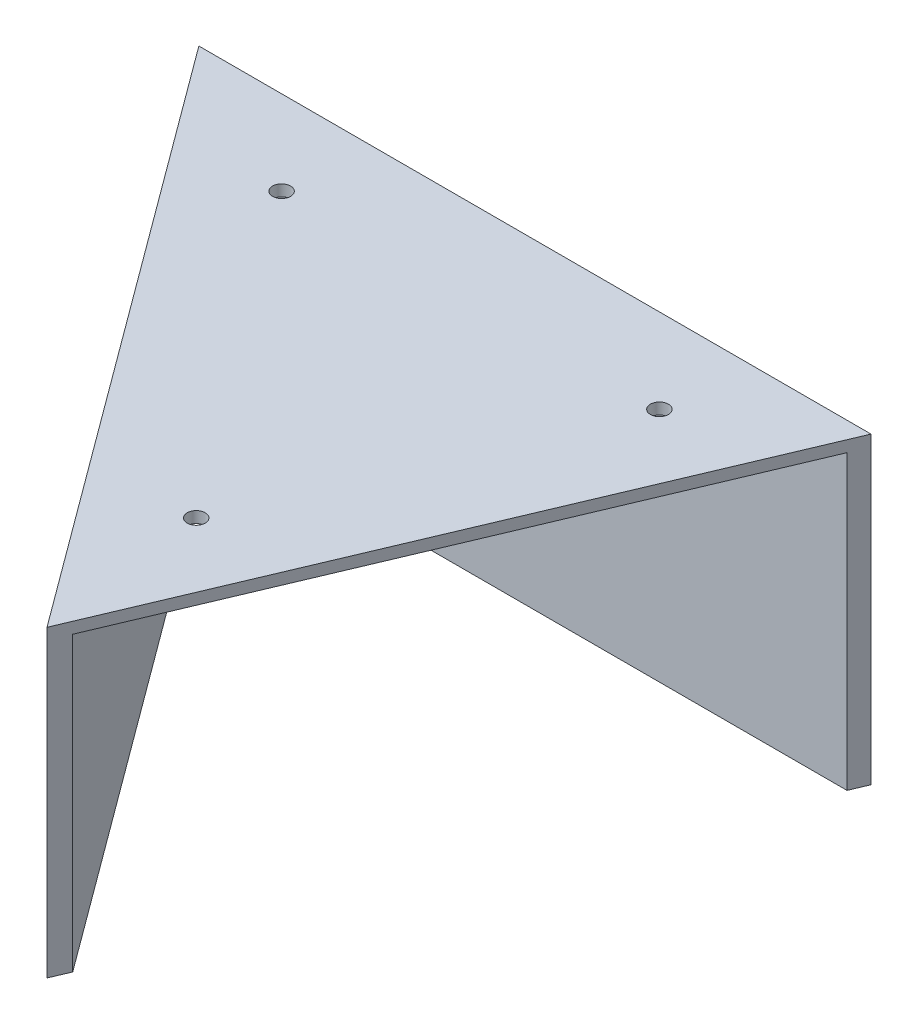
SolidWorks part; units mm, degrees
ref_plane "Front Plane" through (0, 0, 0) normal (0, 0, 1) x (1, 0, 0)
ref_plane "Top Plane" through (0, 0, 0) normal (0, 1, 0) x (1, 0, 0)
ref_plane "Right Plane" through (0, 0, 0) normal (1, 0, 0) x (0, 0, -1)
sketch "Sketch1" plane through (0, 0, 0) normal (0, 1, 0) x (1, 0, 0)
  line L1 (0, 0) -> (-69.5, 0)
  line L3 (6.5, 103) -> (-69.5, 0)
  line L4 (0, 0) -> (40, 0)
  line L6 (40, 0) -> (50, 0)
  line L7 (6.5, 103) -> (50, 0)
extrude "Boss-Extrude1" add sketch "Sketch1" along normal blind 2
sketch "Sketch2" plane through (0, 0, 0) normal (0, -1, 0) x (1, 0, 0)
  line L0 (5.786, -96.9796) -> (45.4764, -3)
  line L1 (45.4764, -3) -> (-63.5581, -3)
  line L2 (-63.5581, -3) -> (5.786, -96.9796)
  line L3 (6.5, -103) -> (50, 0)
  line L4 (50, 0) -> (-69.5, 0)
  line L5 (-69.5, 0) -> (6.5, -103)
  line L7 (50, 0) -> (-69.5, 0)
  line L8 (-69.5, 0) -> (6.5, -103)
  line L12 (6.5, -103) -> (50, 0) construction
  line L13 (6.5, -103) -> (50, 0)
  dimension "D1" = 0
  dimension "D2" = 3
extrude "Boss-Extrude2" add sketch "Sketch2" along normal blind 52
sketch "Sketch4" plane through (0, 0, 0) normal (0, -1, 0) x (1, 0, 0)
  circle A3 centre (-39.7907, -15) radius 1.6
  circle A4 centre (27.3822, -15) radius 1.6
  circle A5 centre (2.9301, -72.898) radius 1.6
extrude "Cut-Extrude3" cut sketch "Sketch4" against normal blind 52
sketch "Sketch6" plane through (0, -52, 0) normal (0, -1, 0) x (1, 0, 0)
  line L0 (5.786, -96.9796) -> (13.5663, -107.5239)
  line L1 (13.5663, -107.5239) -> (48.733, -3)
  line L2 (6.5, -103) -> (50, 0) construction
  line L3 (48.733, -3) -> (45.4764, -3)
  line L4 (45.4764, -3) -> (5.786, -96.9796)
extrude "Cut-Extrude4" cut sketch "Sketch6" against normal up to surface (52 mm away) up to face at (-39.7907, 0, -16.6)
mirror "Mirror1" about plane through (0, 2, 0) normal (0, 0, -1) of bodies 107
delete or keep bodies "Body-Delete/Keep 1" type delete bodies bodies 107
